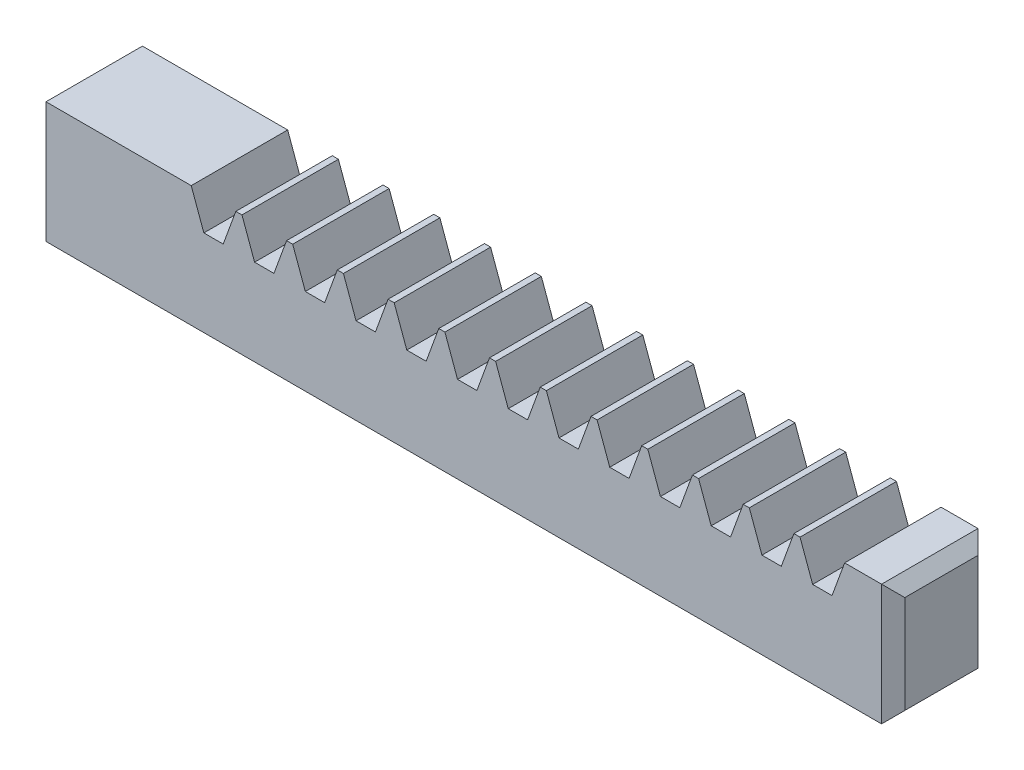
SolidWorks part; units mm, degrees
ref_plane "Front Plane" through (0, 0, 0) normal (0, 0, 1) x (1, 0, 0)
ref_plane "Top Plane" through (0, 0, 0) normal (0, 1, 0) x (1, 0, 0)
ref_plane "Right Plane" through (0, 0, 0) normal (1, 0, 0) x (0, 0, -1)
sketch "Sketch1" plane through (0, 0, 0) normal (1, 0, 0) x (0, 0, -1)
  line L1 (-6.3246, 7.9375) -> (6.3246, 7.9375)
  line L2 (-6.3246, 7.9375) -> (-6.3246, -7.9375)
  line L3 (-6.3246, -7.9375) -> (6.3246, -7.9375)
  line L4 (6.3246, 7.9375) -> (6.3246, -7.9375)
  line L5 (-6.3246, 7.9375) -> (6.3246, -7.9375) construction
  line L6 (-6.3246, -7.9375) -> (6.3246, 7.9375) construction
  point P0 (0, 0)
  dimension "D1" = 12.6492
  dimension "D2" = 15.875
extrude "Boss-Extrude1" add sketch "Sketch1" along normal blind 111.125
hole_wizard "Hole1" positions "Sketch2" profile "Sketch3" legacy
sketch "Sketch2" plane through (0, 0, 0) normal (-1, 0, 0) x (0, 0, 1)
  point P0 (0, 0)
sketch "Sketch3" plane through (0, 0, 0) normal (0, 1, 0) x (0, 0, 1)
  line L0 (0, 0) -> (0, 15.875)
  line L1 (0, 15.875) -> (3.175, 15.875)
  line L2 (3.175, 15.875) -> (3.175, 0)
  line L3 (3.175, 0) -> (0, 0)
  line L4 (0, 110) -> (0, -10) construction
  dimension "Diameter" = 6.35
  dimension "Depth" = 15.875
sketch "Sketch4" plane through (0, 0, 6.3246) normal (0, 0, 1) x (1, 0, 0)
  line L0 (19.05, 7.9375) -> (20.7048, 3.3909)
  line L1 (111.125, 7.9375) -> (0, 7.9375) construction
  line L2 (20.7048, 3.3909) -> (23.2448, 3.3909)
  line L3 (23.2448, 3.3909) -> (24.8997, 7.9375)
  line L4 (21.9748, 3.3909) -> (21.9748, 16.2283) construction
  line L5 (0, 7.9375) -> (0, -7.9375) construction
  point P8 (0, 0)
  dimension "D1" = 40
  dimension "D2" = 2.54
  dimension "D3" = 4.5466
  dimension "D4" = 19.05
extrude "Cut-Extrude1" cut sketch "Sketch4" against normal through all both and the other way through all
pattern_linear "LPattern2" count 13 spacing 6.6548 along (1, 0, 0) of "Cut-Extrude1"
chamfer "Chamfer1" distance 1.524 angle 45 4 edges at (111.125, 0, -6.3246) (111.125, -7.9375, 0) (111.125, 0, 6.3246) (111.125, 7.9375, 0)
